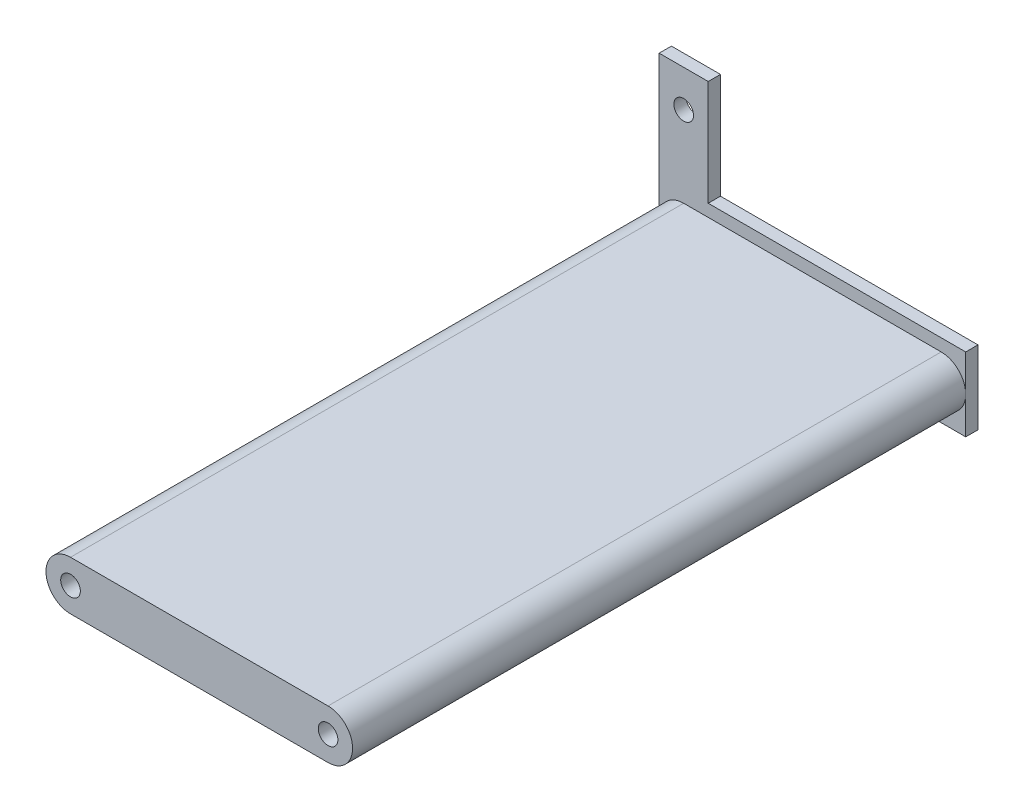
SolidWorks part; units mm, degrees
ref_plane "Front Plane" through (0, 0, 0) normal (0, 0, 1) x (1, 0, 0)
ref_plane "Top Plane" through (0, 0, 0) normal (0, 1, 0) x (1, 0, 0)
ref_plane "Right Plane" through (0, 0, 0) normal (1, 0, 0) x (0, 0, -1)
sketch "Sketch1" plane through (0, 0, 0) normal (0, 0, 1) x (1, 0, 0)
  line L0 (-36.8691, 17.7923) -> (-36.8691, -0.7497)
  line L2 (-36.8691, -0.7497) -> (-5.1191, -0.7497)
  line L5 (-5.1191, -0.7497) -> (-5.1191, 6.8703)
  line L9 (-5.1191, 6.8703) -> (-31.7891, 6.8703)
  line L10 (-31.7891, 6.8703) -> (-31.7891, 17.7923)
  line L11 (-31.7891, 17.7923) -> (-36.8691, 17.7923)
  circle A3 centre (-34.3291, 13.9823) radius 1.016
  circle A4 centre (-34.3291, 3.0603) radius 1.016
  circle A5 centre (-7.6591, 3.0603) radius 1.016
  dimension "D25" = 2.032
  dimension "D3" = 10.922
  dimension "D14" = 3.81
  dimension "D15" = 26.67
  dimension "D16" = 31.75
  dimension "D17" = 3.81
  dimension "D20" = 3.81
  dimension "D21" = 7.62
  dimension "D26" = 10.922
extrude "Boss-Extrude1" add sketch "Sketch1" along normal blind 1.27
sketch "Sketch2" plane through (0, 0, 1.27) normal (0, 0, 1) x (1, 0, 0)
  line L0 (-34.3291, 5.6003) -> (-7.6591, 5.6003)
  line L1 (-34.3291, 0.5203) -> (-7.6591, 0.5203)
  circle A0 centre (-34.3291, 3.0603) radius 1.016
  circle A1 centre (-7.6591, 3.0603) radius 1.016
  arc A2 (-34.3291, 5.6003) -> (-34.3291, 0.5203) centre (-34.3291, 3.0603) ccw
  arc A3 (-7.6591, 0.5203) -> (-7.6591, 5.6003) centre (-7.6591, 3.0603) ccw
extrude "Boss-Extrude3" add sketch "Sketch2" along normal blind 63.5
